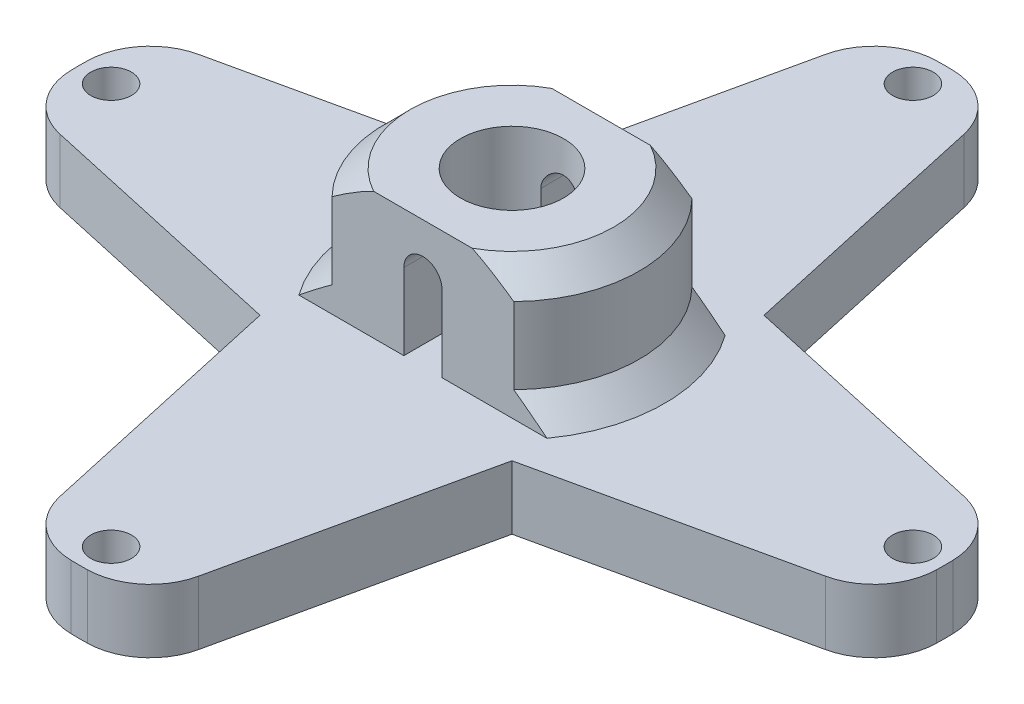
SolidWorks part; units mm, degrees
material "PE Low Density Film"
ref_plane "Front Plane" through (0, 0, 0) normal (0, 0, 1) x (1, 0, 0)
ref_plane "Top Plane" through (0, 0, 0) normal (0, 1, 0) x (1, 0, 0)
ref_plane "Right Plane" through (0, 0, 0) normal (1, 0, 0) x (0, 0, -1)
sketch "Sketch1" plane through (0, 0, 0) normal (0, 1, 0) x (1, 0, 0)
  line L0 (0, 0) -> (0, 31.5) construction
  line L1 (0, 0) -> (31.5, 0) construction
  line L2 (0, 0) -> (0, -31.5) construction
  line L3 (0, 0) -> (-31.5, 0) construction
  circle A0 centre (0, 0) radius 34
  circle A1 centre (0, 31.5) radius 1.6
  circle A2 centre (31.5, 0) radius 1.6
  circle A3 centre (0, -31.5) radius 1.6
  circle A4 centre (-31.5, 0) radius 1.6
  circle A5 centre (0, 0) radius 4.05
  dimension "D1" = 68
  dimension "D3" = 3.2
  dimension "D5" = 8.1
  dimension "D2" = 31.5
  dimension "D4" = 4
extrude "Boss-Extrude1" add sketch "Sketch1" along normal blind 5
sketch "Sketch2" plane through (0, 5, 0) normal (0, 1, 0) x (1, 0, 0)
  line L0 (-7.1414, 7) -> (7.1414, 7)
  line L1 (7.1414, -7) -> (-7.1414, -7)
  arc A0 (-7.1414, 7) -> (-7.1414, -7) centre (0, 0) ccw
  arc A1 (7.1414, -7) -> (7.1414, 7) centre (0, 0) ccw
  circle A2 centre (0, 0) radius 4.05 construction
  circle A3 centre (0, 0) radius 4.05
  dimension "10" = 10
  dimension "D2" = 7
extrude "Boss-Extrude2" add sketch "Sketch2" along normal blind 10
sketch "Sketch3" plane through (0, 0, -7) normal (0, 0, -1) x (-1, 0, 0)
  line L0 (0, 11) -> (0, 5) construction
  line L1 (1.5, 11) -> (1.5, 5)
  line L2 (-1.5, 11) -> (-1.5, 5)
  line L3 (-7.1414, 5) -> (7.1414, 5) construction
  line L4 (-1.5, 5) -> (1.5, 5)
  line L5 (-7.1414, 15) -> (7.1414, 15) construction
  arc A0 (1.5, 11) -> (-1.5, 11) centre (0, 11) ccw
  arc A1 (-1.5, 5) -> (1.5, 5) centre (0, 5) ccw
  point P2 (0, 8)
  dimension "D1" = 1.5
  dimension "D2" = 4
extrude "Cut-Extrude1" cut sketch "Sketch3" against normal through all
sketch "Sketch4" plane through (0, 5, 0) normal (0, 1, 0) x (1, 0, 0)
  line L0 (-33.6822, 4.6381) -> (-9.8995, 9.8995)
  line L1 (-9.8995, 9.8995) -> (-4.6381, 33.6822)
  line L2 (-9.8995, 9.8995) -> (0, 0) construction
  line L3 (0, 0) -> (0, 14.9821) construction
  line L4 (4.6381, 33.6822) -> (9.8995, 9.8995)
  line L5 (9.8995, 9.8995) -> (33.6822, 4.6381)
  line L6 (9.8995, 9.8995) -> (0, 0) construction
  line L7 (33.6822, -4.6381) -> (9.8995, -9.8995)
  line L8 (9.8995, -9.8995) -> (4.6381, -33.6822)
  line L9 (9.8995, -9.8995) -> (0, 0) construction
  line L10 (-4.6381, -33.6822) -> (-9.8995, -9.8995)
  line L11 (-9.8995, -9.8995) -> (-33.6822, -4.6381)
  line L12 (-9.8995, -9.8995) -> (0, 0) construction
  circle A0 centre (-31.5, 0) radius 1.6 construction
  circle A1 centre (0, 0) radius 34
  arc A2 (-4.6381, 33.6822) -> (-33.6822, 4.6381) centre (0, 0) ccw
  arc A3 (33.6822, 4.6381) -> (4.6381, 33.6822) centre (0, 0) ccw
  arc A4 (4.6381, -33.6822) -> (33.6822, -4.6381) centre (0, 0) ccw
  arc A5 (-33.6822, -4.6381) -> (-4.6381, -33.6822) centre (0, 0) ccw
  dimension "D4" = 5
  dimension "D2" = 45
  dimension "D3" = 14
  dimension "D1" = 0
  dimension "D5" = 4
extrude "Cut-Extrude2" cut sketch "Sketch4" against normal blind 10
fillet "Fillet1" radius 5 9 edges at (-4.6381, 2.5, 33.6822) (4.6381, 2.5, 33.6822) (33.6822, 2.5, 4.6381) (33.6822, 2.5, -4.6381) (4.6381, 2.5, -33.6822) (-4.6381, 2.5, -33.6822) (-9.8995, 2.5, -9.8995) (-33.6822, 2.5, 4.6381) (-33.6822, 2.5, -4.6381)
chamfer "Chamfer2" distance 2 angle 45 4 edges at (10, 15, 0) (-10, 15, 0) (-10, 5, 0) (10, 5, 0)
